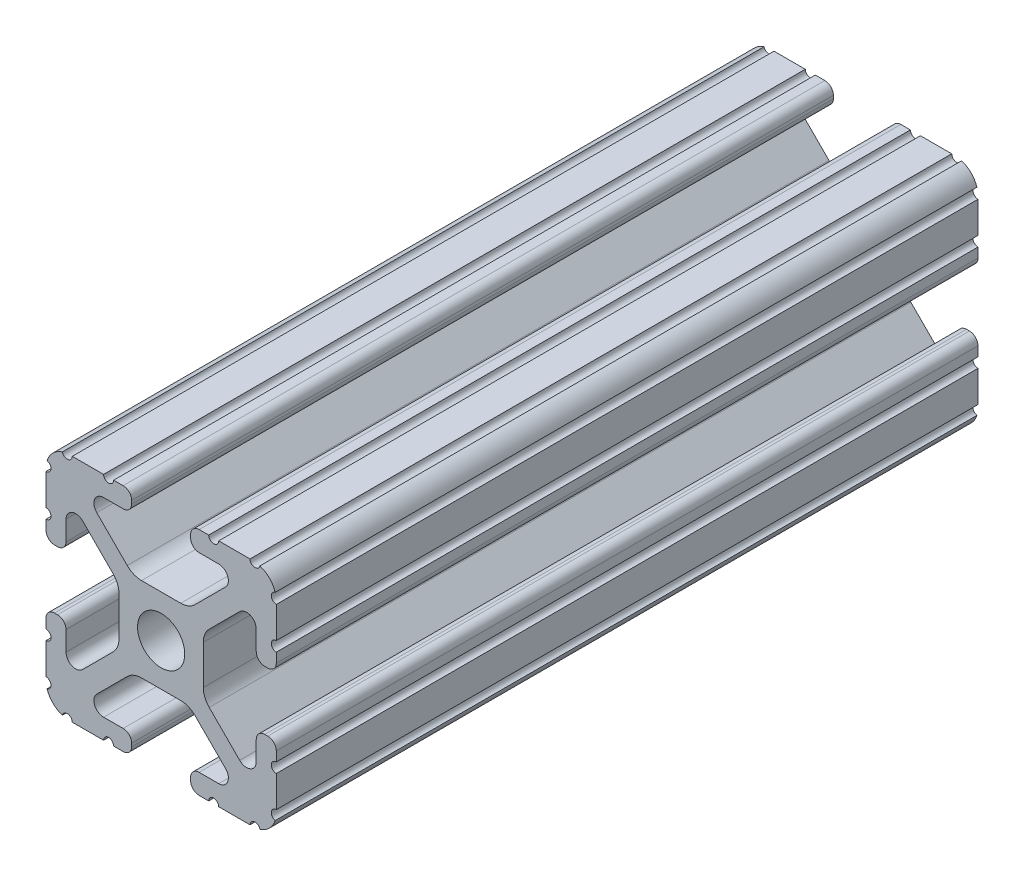
SolidWorks part; units mm, degrees
ref_plane "Front Plane" through (0, 0, 0) normal (0, 0, 1) x (1, 0, 0)
ref_plane "Top Plane" through (0, 0, 0) normal (0, 1, 0) x (1, 0, 0)
ref_plane "Right Plane" through (0, 0, 0) normal (1, 0, 0) x (0, 0, -1)
sketch "Sketch2" plane through (0, 0, 0) normal (0, 0, 1) x (1, 0, 0)
  line L0 (0, 12.7) -> (0, -12.7) construction
  line L1 (-12.7, 0) -> (12.7, 0) construction
  line L2 (3.2512, -12.7) -> (12.7, -12.7)
  line L3 (12.7, -12.7) -> (12.7, -3.2512)
  line L4 (3.2512, -12.7) -> (3.2512, -10.4902)
  line L5 (3.2512, -10.4902) -> (8.9276, -10.4902)
  line L6 (8.9276, -10.4902) -> (3.0856, -4.6482)
  line L7 (0, 0) -> (12.7, -12.7) construction
  line L8 (12.7, -3.2512) -> (10.4902, -3.2512)
  line L9 (10.4902, -3.2512) -> (10.4902, -8.9276)
  line L10 (10.4902, -8.9276) -> (4.6482, -3.0856)
  circle A0 centre (0, 0) radius 2.6035
  arc A1 (6.3485, -10.4902) -> (7.1039, -8.6665) centre (6.3485, -9.4219) ccw construction
  point P8 (0, -4.6482)
  dimension "Center Hole Diameter" = 5.207
  dimension "Rail Height" = 25.4
  dimension "Rail Width" = 25.4
  dimension "T-Slot Width" = 6.5024
  dimension "Slot Inner Width" = 14.8336
  dimension "Thickness" = 2.2098
  dimension "Slot Depth" = 5.842
  dimension "D1" = 2.2098
sketch "Sketch3" plane through (0, 0, 0) normal (1, 0, 0) x (0, 0, -1)
  line L0 (-76.2, -12.7) -> (76.2, -12.7) construction
  line L1 (-68.58, 0) -> (68.58, 0) construction
  dimension "Length" = 152.4
  dimension "D1" = 137.16
sketch "Sketch4" plane through (0, 0, 0) normal (0, 0, 1) x (1, 0, 0)
  line L0 (4.1904, -12.7) -> (10.1173, -12.7)
  line L1 (3.2512, -12.7) -> (12.7, -12.7) construction
  line L2 (3.2512, -12.7) -> (3.2512, -10.4902) construction
  line L3 (3.2512, -10.4902) -> (8.9276, -10.4902) construction
  line L4 (3.2512, -11.4294) -> (3.2512, -11.7608)
  line L5 (4.1904, -10.4902) -> (6.3485, -10.4902)
  line L6 (0, -4.6482) -> (2.164, -4.6482)
  line L7 (8.9276, -10.4902) -> (3.0856, -4.6482) construction
  line L8 (3.7373, -5.2999) -> (7.1039, -8.6665)
  line L9 (12.7, -12.7) -> (12.7, -3.2512) construction
  line L10 (10.4902, -8.9276) -> (4.6482, -3.0856) construction
  line L11 (10.4902, -3.2512) -> (10.4902, -8.9276) construction
  line L12 (10.4902, -6.3485) -> (10.4902, -4.1904)
  line L13 (12.7, -3.2512) -> (10.4902, -3.2512) construction
  line L14 (11.4294, -3.2512) -> (11.7608, -3.2512)
  line L15 (12.7, -4.1904) -> (12.7, -10.1173)
  line L16 (8.6665, -7.1039) -> (5.2999, -3.7373)
  line L17 (4.6482, 0) -> (4.6482, -2.164)
  line L18 (-12.7, 0) -> (12.7, 0) construction
  line L19 (0, -4.6482) -> (0, -2.6035)
  line L20 (0, 12.7) -> (0, -12.7) construction
  line L21 (4.6482, 0) -> (2.6035, 0)
  arc A0 (3.2512, -11.7608) -> (4.1904, -12.7) centre (4.1904, -11.7608) ccw
  arc A2 (3.2512, -11.4294) -> (4.1904, -10.4902) centre (4.1904, -11.4294) cw
  arc A3 (6.3485, -10.4902) -> (7.1039, -8.6665) centre (6.3485, -9.4219) ccw
  arc A4 (2.164, -4.6482) -> (3.7373, -5.2999) centre (2.164, -6.8732) cw
  arc A5 (10.1173, -12.7) -> (12.7, -10.1173) centre (10.1173, -10.1173) ccw
  arc A6 (8.6665, -7.1039) -> (10.4902, -6.3485) centre (9.4219, -6.3485) ccw
  arc A7 (10.4902, -4.1904) -> (11.4294, -3.2512) centre (11.4294, -4.1904) cw
  arc A8 (11.7608, -3.2512) -> (12.7, -4.1904) centre (11.7608, -4.1904) cw
  arc A9 (5.2999, -3.7373) -> (4.6482, -2.164) centre (6.8732, -2.164) cw
  circle A10 centre (0, 0) radius 2.6035 construction
  arc A11 (0, -2.6035) -> (2.6035, 0) centre (0, 0) ccw
  dimension "D1" = 2.5827
  dimension "D2" = 2.225
  dimension "D3" = 0.9392
extrude "Boss-Extrude1" add sketch "Sketch4" along normal mid plane 77.4
sketch "Sketch5" plane through (0, 0, 0) normal (0, 0, 1) x (1, 0, 0)
  line L0 (3.2512, -12.7) -> (12.7, -12.7) construction
  line L1 (4.1904, -10.4902) -> (6.3485, -10.4902) construction
  line L3 (0, 0) -> (12.7, -12.7) construction
  line L4 (6.3485, -10.4902) -> (6.3485, -12.7) construction
  line L5 (8.9276, -10.4902) -> (3.0856, -4.6482) construction
  circle A0 centre (10.3562, -12.7) radius 0.5524
  circle A1 centre (5.796, -12.7) radius 0.5524
  circle A2 centre (12.7, -10.3562) radius 0.5524
  circle A3 centre (12.7, -5.796) radius 0.5524
  point P10 (5.2694, -10.4902)
  point P12 (9.4219, -6.3485)
  dimension "D1" = 1.1049
extrude "Cut-Extrude1" cut sketch "Sketch5" against normal through all both and the other way through all
mirror "Mirror1" about plane through (0, 0, 0) normal (1, 0, 0) of bodies 137 134
mirror "Mirror2" about plane through (0, 0, 0) normal (0, 1, 0) of bodies 135
sketch "Sketch6" plane through (0, 0, 0) normal (0, 1, 0) x (1, 0, 0)
  line L0 (0, 38.7) -> (0, 26) construction
  line L1 (0, -38.7) -> (0, -26) construction
  line L4 (2.164, 38.7) -> (-2.164, 38.7)
  line L5 (-2.164, 38.7) -> (-2.164, -38.7)
  line L6 (-2.164, -38.7) -> (2.164, -38.7)
  line L7 (2.164, -38.7) -> (2.164, 38.7)
  line L8 (2.164, 38.7) -> (-2.164, 38.7) construction
  line L9 (-2.164, 38.7) -> (-2.164, -38.7) construction
  line L10 (-2.164, -38.7) -> (2.164, -38.7) construction
  line L11 (2.164, -38.7) -> (2.164, 38.7) construction
  circle A0 centre (0, -26) radius 2.555
  circle A1 centre (0, 26) radius 2.555
  dimension "D2" = 12.7
  dimension "D3" = 5.11
  dimension "D1" = 0
extrude "Cut-Extrude2" [suppressed] cut sketch "Sketch6" against normal through all both and the other way through all
sketch "Sketch7" plane through (0, 0, 0) normal (1, 0, 0) x (0, 0, -1)
  line L0 (-38.7, 0) -> (-13.3, 0) construction
  line L1 (-38.7, -2.164) -> (38.7, -2.164) construction
  line L6 (-38.7, -2.164) -> (-38.7, 2.164) construction
  line L7 (-38.7, 2.164) -> (38.7, 2.164) construction
  line L8 (38.7, -2.164) -> (38.7, 2.164) construction
  line L9 (-38.7, -2.164) -> (38.7, 2.164) construction
  line L10 (-38.7, 2.164) -> (38.7, -2.164) construction
  line L11 (38.7, 0) -> (13.3, 0) construction
  circle A2 centre (13.3, 0) radius 2.54
  circle A3 centre (-13.3, 0) radius 2.54
  point P0 (0, 0)
  dimension "D1" = 25.4
  dimension "D2" = 5.08
extrude "Cut-Extrude3" [suppressed] cut sketch "Sketch7" against normal through all both and the other way through all
equation "\"D1@Boss-Extrude1\"= 7.74cm"
equation "\"D1@Sketch2\"=\"Thickness@Sketch2\""
equation "\"D2@Sketch4\"=\"Slot Inner Width@Sketch2\"*0.15"
equation "\"D1@Sketch4\"=\"D3@Sketch4\"*2.75"
equation "\"D3@Sketch4\"=\"Thickness@Sketch2\"*0.425"
equation "\"D1@Sketch5\"=\"Thickness@Sketch2\"*0.5"
equation "\"D1@Sketch3\"=\"Length@Sketch3\"*0.9"
